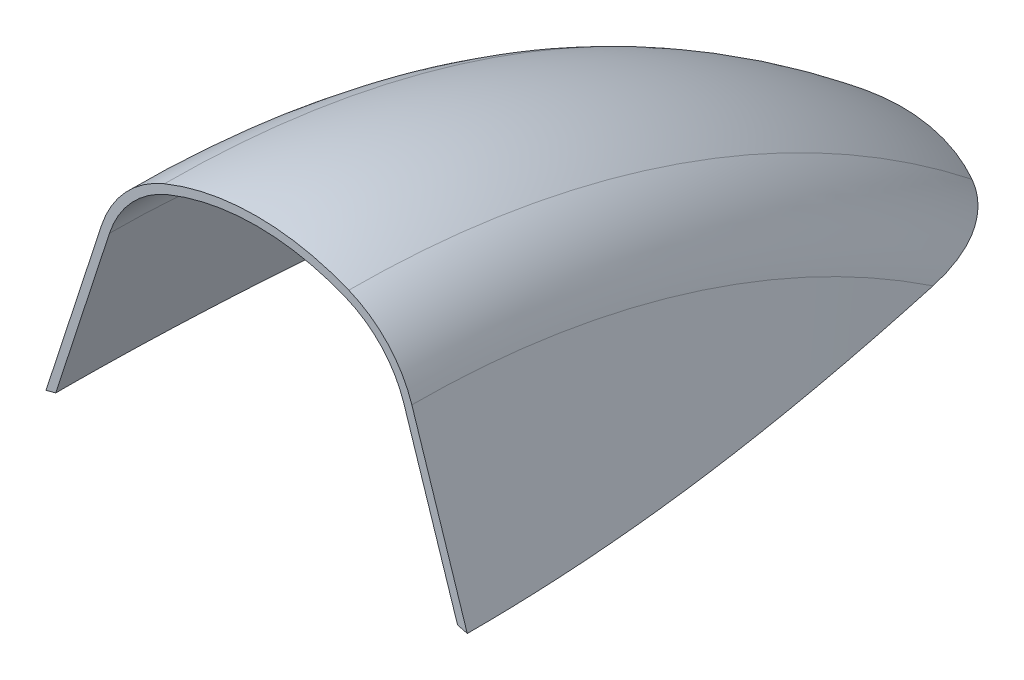
SolidWorks part; units mm, degrees
ref_plane "Front Plane" through (0, 0, 0) normal (0, 0, 1) x (1, 0, 0)
ref_plane "Top Plane" through (0, 0, 0) normal (0, 1, 0) x (1, 0, 0)
ref_plane "Right Plane" through (0, 0, 0) normal (1, 0, 0) x (0, 0, -1)
sketch "Sketch1" plane through (0, 0, 0) normal (0, 0, 1) x (1, 0, 0)
  line L0 (0, 0) -> (0, 324.652) construction
  line L1 (30.7076, 181.3003) -> (24.6961, 151.9943) construction
  line L2 (37.137, 149.4423) -> (40.6988, 166.8059) construction
  line L3 (-37.137, 149.4423) -> (-40.6988, 166.8059) construction
  line L4 (-30.7076, 181.3003) -> (-24.6961, 151.9943) construction
  line L5 (0, 0) -> (-38.8975, 189.6253) construction
  line L6 (27.6276, 178.6698) -> (37.137, 149.4423) construction
  line L7 (0, 0) -> (38.8975, 189.6253) construction
  line L12 (30.2004, 175.8931) -> (45.4337, 129.0731) construction
  line L13 (-27.6276, 178.6698) -> (-37.137, 149.4423) construction
  line L14 (-30.2004, 175.8931) -> (-45.4337, 129.0731) construction
  line L51 (29.1372, 179.161) -> (39.5422, 147.1807)
  line L54 (-29.1372, 179.161) -> (-39.5422, 147.1807)
  line L55 (0, 2.54) -> (-211.9582, 2.54) construction
  line L56 (-37.7172, 147.659) -> (-27.6276, 178.6698)
  line L57 (37.7172, 147.659) -> (27.6276, 178.6698)
  circle A0 centre (0, 0) radius 152.4 construction
  circle A1 centre (9.5123, 172.7758) radius 12.7 construction
  circle A2 centre (9.5123, 172.7758) radius 19.05 construction
  circle A3 centre (-15.875, 171.9727) radius 6.35 construction
  circle A4 centre (-15.875, 171.9727) radius 12.7 construction
  circle A5 centre (0, 0) radius 153.9875 construction
  circle A8 centre (0, 149.4423) radius 44.248 construction
  circle A10 centre (0, 149.4423) radius 45.8355 construction
  circle A38 centre (15.875, 171.9727) radius 12.7 construction
  circle A39 centre (15.875, 171.9727) radius 6.35 construction
  arc A49 (17.303, 191.8864) -> (-17.303, 191.8864) centre (0, 149.4423) ccw
  arc A50 (29.1372, 179.161) -> (17.303, 191.8864) centre (9.5123, 172.7758) ccw
  arc A51 (-29.1372, 179.161) -> (-17.303, 191.8864) centre (-9.5123, 172.7758) cw
  arc A54 (39.5422, 147.1807) -> (37.7172, 147.659) centre (0, 0) ccw
  arc A55 (-16.7037, 190.4163) -> (-27.6276, 178.6698) centre (-9.5123, 172.7758) ccw
  arc A57 (16.7037, 190.4163) -> (-16.7037, 190.4163) centre (0, 149.4423) ccw
  arc A59 (-37.7172, 147.659) -> (-39.5422, 147.1807) centre (0, 0) ccw
  arc A60 (16.7037, 190.4163) -> (27.6276, 178.6698) centre (9.5123, 172.7758) cw
  dimension "D1" = 304.8
  dimension "D2" = 25.4
  dimension "D3" = 15.875
  dimension "D4" = 38.1
  dimension "D5" = 12.7
  dimension "D6" = 9.5123
  dimension "D8" = 307.975
  dimension "D7" = 152.4
  dimension "D11" = 88.496
  dimension "D12" = 91.671
  dimension "D13" = 1.5875
  dimension "D14" = 20.6375
  dimension "D16" = 19.05
  dimension "D9" = 6.35
  dimension "D10" = 6.35
  dimension "D15" = 2.54
revolve "Revolve1" add sketch "Sketch1" angle 56 about L55
sketch "Sketch2" plane through (0, 0, 0) normal (0, 0, 1) x (1, 0, 0)
  circle A0 centre (0, 0) radius 152.4
  dimension "D1" = 304.8
extrude "Cut-Extrude1" cut sketch "Sketch2" against normal blind 309.88
